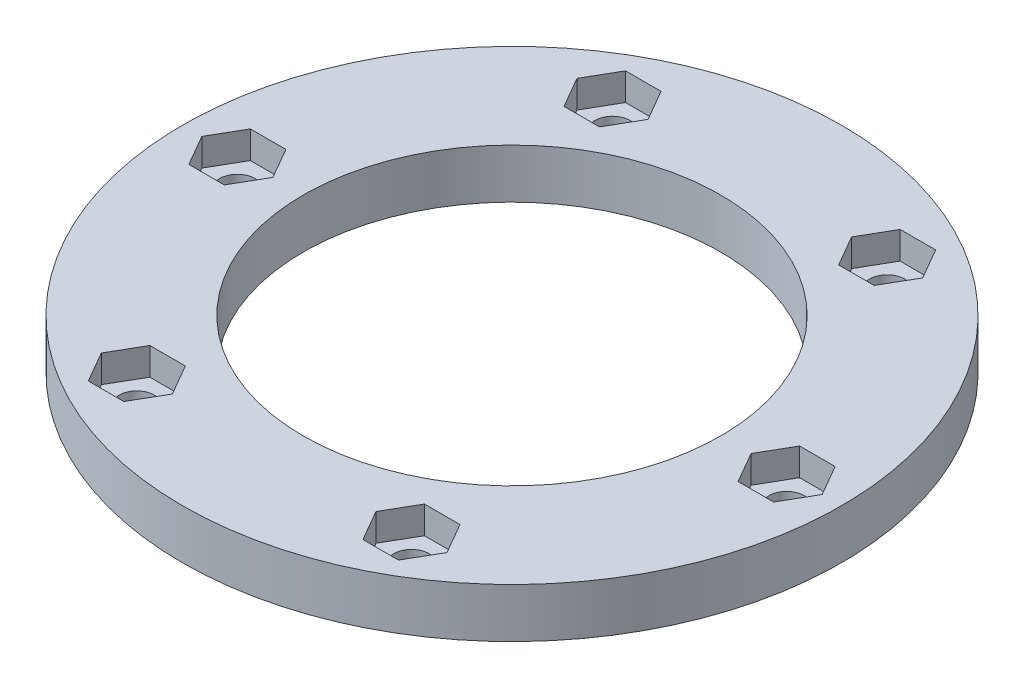
SolidWorks part; units mm, degrees
ref_plane "Front Plane" through (0, 0, 0) normal (0, 0, 1) x (1, 0, 0)
ref_plane "Top Plane" through (0, 0, 0) normal (0, 1, 0) x (1, 0, 0)
ref_plane "Right Plane" through (0, 0, 0) normal (1, 0, 0) x (0, 0, -1)
sketch "Sketch1" plane through (0, 0, 0) normal (0, 1, 0) x (1, 0, 0)
  circle A0 centre (0, 0) radius 19
  circle A1 centre (0, 0) radius 30
  circle A2 centre (25, 0) radius 1.6
  circle A3 centre (12.5, -21.6506) radius 1.6
  circle A4 centre (-12.5, -21.6506) radius 1.6
  circle A5 centre (-25, 0) radius 1.6
  circle A6 centre (-12.5, 21.6506) radius 1.6
  circle A7 centre (12.5, 21.6506) radius 1.6
  point P18 (0, 0)
  dimension "D1" = 38
  dimension "D2" = 60
  dimension "D4" = 3.2
  dimension "D3" = 25
  dimension "D5" = 6
extrude "Boss-Extrude1" add sketch "Sketch1" along normal blind 2
sketch "Sketch2" plane through (0, 2, 0) normal (0, 1, 0) x (1, 0, 0)
  line L0 (14.1166, -24.4506) -> (15.7332, -21.6506)
  line L1 (28.2332, 0) -> (26.6166, 2.8)
  line L2 (26.6166, 2.8) -> (23.3834, 2.8)
  line L3 (23.3834, 2.8) -> (21.7668, 0)
  line L4 (21.7668, 0) -> (23.3834, -2.8)
  line L5 (23.3834, -2.8) -> (26.6166, -2.8)
  line L6 (26.6166, -2.8) -> (28.2332, 0)
  line L7 (15.7332, -21.6506) -> (14.1166, -18.8506)
  line L8 (14.1166, -18.8506) -> (10.8834, -18.8506)
  line L9 (10.8834, -18.8506) -> (9.2668, -21.6506)
  line L10 (9.2668, -21.6506) -> (10.8834, -24.4506)
  line L11 (10.8834, -24.4506) -> (14.1166, -24.4506)
  line L12 (-14.1166, -24.4506) -> (-10.8834, -24.4506)
  line L13 (-10.8834, -24.4506) -> (-9.2668, -21.6506)
  line L14 (-9.2668, -21.6506) -> (-10.8834, -18.8506)
  line L15 (-10.8834, -18.8506) -> (-14.1166, -18.8506)
  line L16 (-14.1166, -18.8506) -> (-15.7332, -21.6506)
  line L17 (-15.7332, -21.6506) -> (-14.1166, -24.4506)
  line L18 (-28.2332, 0) -> (-26.6166, -2.8)
  line L19 (-26.6166, -2.8) -> (-23.3834, -2.8)
  line L20 (-23.3834, -2.8) -> (-21.7668, 0)
  line L21 (-21.7668, 0) -> (-23.3834, 2.8)
  line L22 (-23.3834, 2.8) -> (-26.6166, 2.8)
  line L23 (-26.6166, 2.8) -> (-28.2332, 0)
  line L24 (-14.1166, 24.4506) -> (-15.7332, 21.6506)
  line L25 (-15.7332, 21.6506) -> (-14.1166, 18.8506)
  line L26 (-14.1166, 18.8506) -> (-10.8834, 18.8506)
  line L27 (-10.8834, 18.8506) -> (-9.2668, 21.6506)
  line L28 (-9.2668, 21.6506) -> (-10.8834, 24.4506)
  line L29 (-10.8834, 24.4506) -> (-14.1166, 24.4506)
  line L30 (14.1166, 24.4506) -> (10.8834, 24.4506)
  line L31 (10.8834, 24.4506) -> (9.2668, 21.6506)
  line L32 (9.2668, 21.6506) -> (10.8834, 18.8506)
  line L33 (10.8834, 18.8506) -> (14.1166, 18.8506)
  line L34 (14.1166, 18.8506) -> (15.7332, 21.6506)
  line L35 (15.7332, 21.6506) -> (14.1166, 24.4506)
  circle A0 centre (0, 0) radius 19 construction
  circle A1 centre (0, 0) radius 19 construction
  circle A2 centre (25, 0) radius 1.6 construction
  circle A3 centre (25, 0) radius 1.6 construction
  circle A4 centre (25, 0) radius 2.8 construction
  circle A5 centre (0, 0) radius 19 construction
  circle A6 centre (0, 0) radius 30
  circle A7 centre (0, 0) radius 30
  circle A8 centre (0, 0) radius 19
  point P6 (25, -2.8)
  point P46 (0, 0)
  dimension "D1" = 5.6
  dimension "D3" = 0
  dimension "D2" = 6
extrude "Boss-Extrude3" add sketch "Sketch2" along normal blind 2.5
